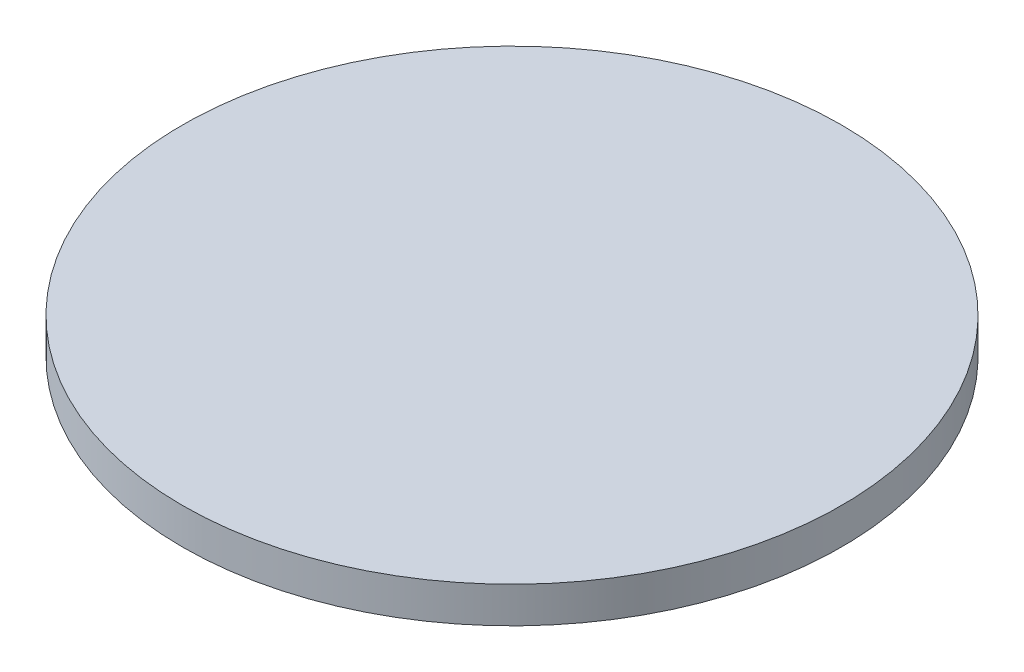
SolidWorks part; units mm, degrees
ref_plane "Front Plane" through (0, 0, 0) normal (0, 0, 1) x (1, 0, 0)
ref_plane "Top Plane" through (0, 0, 0) normal (0, 1, 0) x (1, 0, 0)
ref_plane "Right Plane" through (0, 0, 0) normal (1, 0, 0) x (0, 0, -1)
sketch "Sketch1" plane through (0, 0, 0) normal (0, 1, 0) x (1, 0, 0)
  circle A0 centre (0, 0) radius 64
  dimension "D1" = 128
extrude "Boss-Extrude1" add sketch "Sketch1" along normal blind 7
